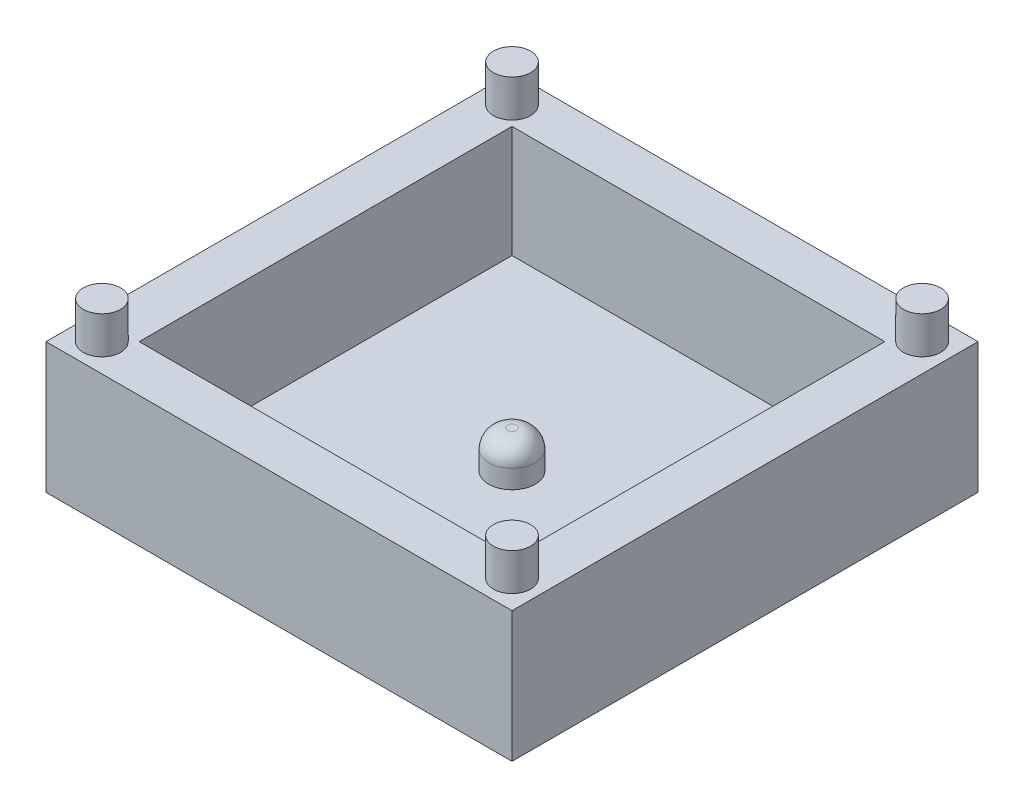
SolidWorks part; units mm, degrees
ref_plane "Front Plane" through (0, 0, 0) normal (0, 0, 1) x (1, 0, 0)
ref_plane "Top Plane" through (0, 0, 0) normal (0, 1, 0) x (1, 0, 0)
ref_plane "Right Plane" through (0, 0, 0) normal (1, 0, 0) x (0, 0, -1)
sketch "Sketch1" plane through (0, 0, 0) normal (0, 1, 0) x (1, 0, 0)
  line L1 (-12.5, -12.5) -> (12.5, -12.5)
  line L2 (-12.5, -12.5) -> (-12.5, 12.5)
  line L3 (-12.5, 12.5) -> (12.5, 12.5)
  line L4 (12.5, -12.5) -> (12.5, 12.5)
  line L5 (-12.5, -12.5) -> (12.5, 12.5) construction
  line L6 (-12.5, 12.5) -> (12.5, -12.5) construction
  point P0 (0, 0)
  dimension "D1" = 25
  dimension "D2" = 25
extrude "Boss-Extrude1" add sketch "Sketch1" along normal blind 7
sketch "Sketch2" plane through (0, 7, 0) normal (0, 1, 0) x (1, 0, 0)
  line L1 (-10, -10) -> (10, -10)
  line L2 (-10, -10) -> (-10, 10)
  line L3 (-10, 10) -> (10, 10)
  line L4 (10, -10) -> (10, 10)
  line L5 (-10, -10) -> (10, 10) construction
  line L6 (-10, 10) -> (10, -10) construction
  point P0 (0, 0)
  dimension "D1" = 20
  dimension "D2" = 20
extrude "Cut-Extrude1" cut sketch "Sketch2" against normal blind 6
sketch "Sketch3" plane through (0, 1, 0) normal (0, 1, 0) x (1, 0, 0)
  circle A0 centre (0, 0) radius 1.25
  dimension "D1" = 2.5
extrude "Boss-Extrude2" add sketch "Sketch3" along normal blind 2
fillet "Fillet1" radius 1 1 edges at (0, 3, 1.25)
sketch "Sketch4" plane through (0, 7, 0) normal (0, 1, 0) x (1, 0, 0)
  line L0 (-12.5, -12.5) -> (12.5, -12.5) construction
  line L1 (12.5, -12.5) -> (12.5, 12.5) construction
  line L2 (12.5, 12.5) -> (-12.5, 12.5) construction
  line L3 (-12.5, 12.5) -> (-12.5, -12.5) construction
  circle A0 centre (-11, 11) radius 1
  circle A1 centre (11, 11) radius 1
  circle A2 centre (11, -11) radius 1
  circle A3 centre (-11, -11) radius 1
  dimension "D1" = 2
  dimension "D4" = 2
  dimension "D7" = 2
  dimension "D10" = 2
  dimension "D2" = 1.5
  dimension "D3" = 1.5
  dimension "D5" = 1.5
  dimension "D6" = 1.5
  dimension "D8" = 1.5
  dimension "D9" = 1.5
  dimension "D11" = 1.5
  dimension "D12" = 1.5
extrude "Boss-Extrude3" add sketch "Sketch4" along normal blind 2
